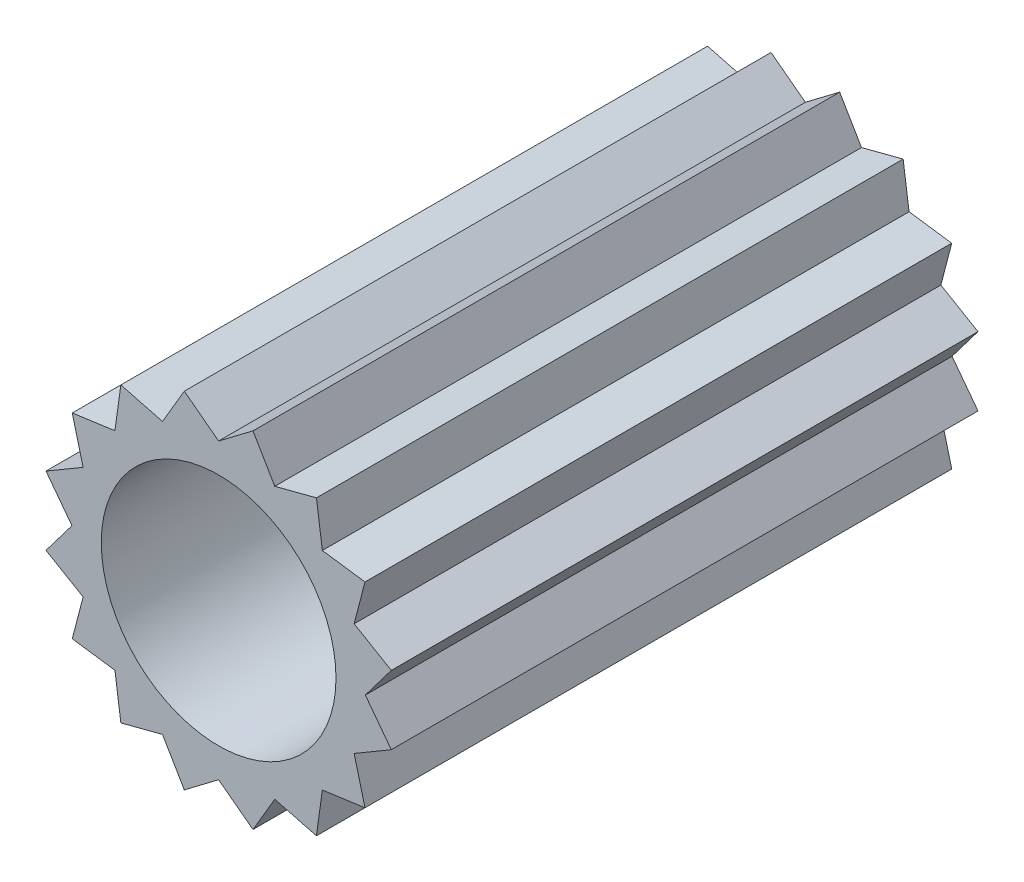
SolidWorks part; units mm, degrees
ref_plane "Front Plane" through (0, 0, 0) normal (0, 0, 1) x (1, 0, 0)
ref_plane "Top Plane" through (0, 0, 0) normal (0, 1, 0) x (1, 0, 0)
ref_plane "Right Plane" through (0, 0, 0) normal (1, 0, 0) x (0, 0, -1)
sketch "Sketch2" plane through (0, 0, 0) normal (0, 0, 1) x (1, 0, 0)
  line L0 (-3, 0) -> (3, 0) construction
  line L1 (0, 3) -> (0, -3) construction
  line L2 (2.1213, 2.1213) -> (-2.1213, -2.1213) construction
  line L3 (1.1481, 2.7716) -> (0, 0) construction
  line L4 (0, 2.5) -> (0.5853, 2.9424)
  line L5 (0.5853, 2.9424) -> (0.9567, 2.3097)
  line L6 (0, 0) -> (0.5853, 2.9424) construction
  line L7 (0.9567, 2.3097) -> (1.6667, 2.4944)
  line L8 (1.6667, 2.4944) -> (1.7678, 1.7678)
  line L9 (1.7678, 1.7678) -> (2.4944, 1.6667)
  line L10 (2.4944, 1.6667) -> (2.3097, 0.9567)
  line L11 (2.3097, 0.9567) -> (2.9424, 0.5853)
  line L12 (2.9424, 0.5853) -> (2.5, 0)
  line L13 (2.5, 0) -> (2.9424, -0.5853)
  line L14 (2.9424, -0.5853) -> (2.3097, -0.9567)
  line L15 (2.3097, -0.9567) -> (2.4944, -1.6667)
  line L16 (2.4944, -1.6667) -> (1.7678, -1.7678)
  line L17 (1.7678, -1.7678) -> (1.6667, -2.4944)
  line L18 (1.6667, -2.4944) -> (0.9567, -2.3097)
  line L19 (0.9567, -2.3097) -> (0.5853, -2.9424)
  line L20 (0.5853, -2.9424) -> (0, -2.5)
  line L21 (0, -2.5) -> (-0.5853, -2.9424)
  line L22 (-0.5853, -2.9424) -> (-0.9567, -2.3097)
  line L23 (-0.9567, -2.3097) -> (-1.6667, -2.4944)
  line L24 (-1.6667, -2.4944) -> (-1.7678, -1.7678)
  line L25 (-1.7678, -1.7678) -> (-2.4944, -1.6667)
  line L26 (-2.4944, -1.6667) -> (-2.3097, -0.9567)
  line L27 (-2.3097, -0.9567) -> (-2.9424, -0.5853)
  line L28 (-2.9424, -0.5853) -> (-2.5, 0)
  line L29 (-2.5, 0) -> (-2.9424, 0.5853)
  line L30 (-2.9424, 0.5853) -> (-2.3097, 0.9567)
  line L31 (-2.3097, 0.9567) -> (-2.4944, 1.6667)
  line L32 (-2.4944, 1.6667) -> (-1.7678, 1.7678)
  line L33 (-1.7678, 1.7678) -> (-1.6667, 2.4944)
  line L34 (-1.6667, 2.4944) -> (-0.9567, 2.3097)
  line L35 (-0.9567, 2.3097) -> (-0.5853, 2.9424)
  line L36 (-0.5853, 2.9424) -> (0, 2.5)
  circle A0 centre (0, 0) radius 2
  circle A1 centre (0, 0) radius 3 construction
  circle A2 centre (0, 0) radius 2.5 construction
  point P4 (0, 0)
  point P64 (0, 0)
  dimension "D1" = 4
  dimension "D2" = 6
  dimension "D3" = 5
  dimension "D4" = 45
  dimension "D5" = 22.5
  dimension "D6" = 11.25
  dimension "D7" = 16
extrude "Boss-Extrude1" add sketch "Sketch2" along normal blind 10
